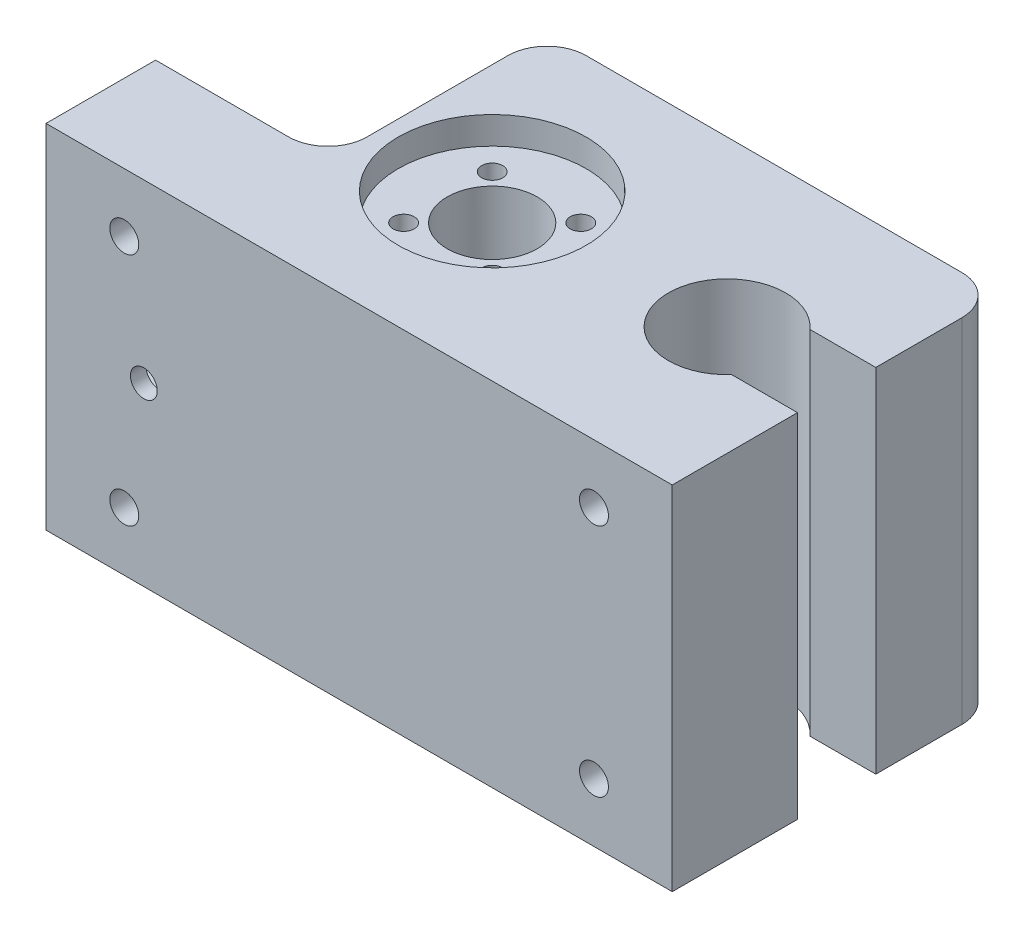
SolidWorks part; units mm, degrees
ref_plane "Front Plane" through (0, 0, 0) normal (0, 0, 1) x (1, 0, 0)
ref_plane "Top Plane" through (0, 0, 0) normal (0, 1, 0) x (1, 0, 0)
ref_plane "Right Plane" through (0, 0, 0) normal (1, 0, 0) x (0, 0, -1)
sketch "Sketch1" plane through (0, 0, 0) normal (0, 0, 1) x (1, 0, 0)
  line L0 (80, 22.5) -> (0, 22.5) construction
  line L1 (0, 0) -> (80, 0)
  line L2 (0, 0) -> (0, 45)
  line L3 (0, 45) -> (80, 45)
  line L4 (80, 0) -> (80, 45)
  dimension "D1" = 80
  dimension "D2" = 45
extrude "Boss-Extrude1" add sketch "Sketch1" along normal blind 42
sketch "Sketch3" plane through (0, 45, 0) normal (0, 1, 0) x (1, 0, 0)
  line L0 (0, -28) -> (22, -28)
  line L1 (0, -42) -> (0, 0) construction
  line L2 (22, -28) -> (22, 0)
  line L3 (80, 0) -> (0, 0) construction
  line L4 (22, 0) -> (0, 0)
  line L5 (0, 0) -> (0, -28)
  dimension "D1" = 28
  dimension "D2" = 22
extrude "Cut-Extrude2" cut sketch "Sketch3" against normal through all
sketch "Sketch4" plane through (0, 0, 0) normal (-1, 0, 0) x (0, 0, 1)
  line L0 (42, 45) -> (42, 0) construction
  line L1 (30, 31) -> (40, 31)
  line L2 (30, 31) -> (30, 14)
  line L3 (30, 14) -> (40, 14)
  line L4 (40, 31) -> (40, 14)
  line L5 (28, 0) -> (28, 45) construction
  line L6 (42, 45) -> (28, 45) construction
  dimension "D1" = 17
  dimension "D2" = 2
  dimension "D3" = 2
  dimension "D4" = 14
extrude "Cut-Extrude3" cut sketch "Sketch4" against normal blind 28
sketch "Sketch7" plane through (0, 45, 0) normal (0, 1, 0) x (1, 0, 0)
  circle A0 centre (36, -21) radius 12
  dimension "D1" = 24
extrude "Cut-Extrude5" cut sketch "Sketch7" against normal blind 3.5 contours A0
sketch "Sketch11" plane through (0, 41.5, 0) normal (0, 1, 0) x (1, 0, 0)
  circle A0 centre (41.6569, -15.3431) radius 1.35
  circle A1 centre (41.6569, -26.6569) radius 1.35
  circle A2 centre (30.3431, -26.6569) radius 1.35
  circle A3 centre (30.3431, -15.3431) radius 1.35
  dimension "D1" = 2.7
extrude "Cut-Extrude6" cut sketch "Sketch11" against normal blind 15
sketch "Sketch12" plane through (0, 41.5, 0) normal (0, 1, 0) x (1, 0, 0)
  circle A0 centre (36, -21) radius 5.75
  dimension "D1" = 11.5
extrude "Cut-Extrude7" cut sketch "Sketch12" against normal through all contours A0
sketch "Sketch13" plane through (0, 45, 0) normal (0, 1, 0) x (1, 0, 0)
  circle A0 centre (66, -21) radius 7.5
  dimension "D1" = 15
extrude "Cut-Extrude8" cut sketch "Sketch13" against normal through all
sketch "Sketch14" plane through (0, 45, 0) normal (0, 1, 0) x (1, 0, 0)
  line L0 (66, -21) -> (80, -21) construction
  line L1 (80, -42) -> (80, 0) construction
  line L3 (67.9005, -26) -> (80, -26)
  line L4 (67.9005, -26) -> (67.9005, -16)
  line L5 (67.9005, -16) -> (80, -16)
  line L6 (80, -26) -> (80, -16)
  line L7 (67.9005, -26) -> (80, -16) construction
  line L8 (67.9005, -16) -> (80, -26) construction
  point P5 (73.9502, -21)
  dimension "D1" = 10
extrude "Cut-Extrude9" cut sketch "Sketch14" against normal through all
sketch "Sketch15" plane through (0, 0, 42) normal (0, 0, 1) x (1, 0, 0)
  circle A0 centre (12.5, 22.5) radius 1.7123
extrude "Cut-Extrude10" cut sketch "Sketch15" against normal through all
sketch "Sketch16" plane through (0, 0, 42) normal (0, 0, 1) x (1, 0, 0)
  line L0 (80, 22.5) -> (0, 22.5) construction
  line L1 (80, 0) -> (80, 45) construction
  line L2 (0, 45) -> (0, 0) construction
  line L4 (70, 7.5) -> (10, 7.5) construction
  line L5 (70, 7.5) -> (70, 37.5) construction
  line L6 (70, 37.5) -> (10, 37.5) construction
  line L7 (10, 7.5) -> (10, 37.5) construction
  line L8 (70, 7.5) -> (10, 37.5) construction
  line L9 (70, 37.5) -> (10, 7.5) construction
  circle A0 centre (10, 37.5) radius 1.85
  circle A1 centre (70, 37.5) radius 1.85
  circle A2 centre (70, 7.5) radius 1.85
  circle A3 centre (10, 7.5) radius 1.85
  point P6 (40, 22.5)
  dimension "D3" = 3.7
  dimension "D4" = 3.7
  dimension "D5" = 3.7
  dimension "D6" = 3.7
  dimension "D1" = 30
  dimension "D2" = 60
extrude "Cut-Extrude11" cut sketch "Sketch16" against normal blind 8
fillet "Fillet2" radius 5 3 edges at (22, 22.5, 28) (22, 22.5, 0) (80, 22.5, 0)
sketch "Sketch17" plane through (0, 0, 0) normal (0, -1, 0) x (1, 0, 0)
  circle A0 centre (36, 21) radius 12.5
  dimension "D1" = 25
extrude "Cut-Extrude12" cut sketch "Sketch17" against normal blind 31
